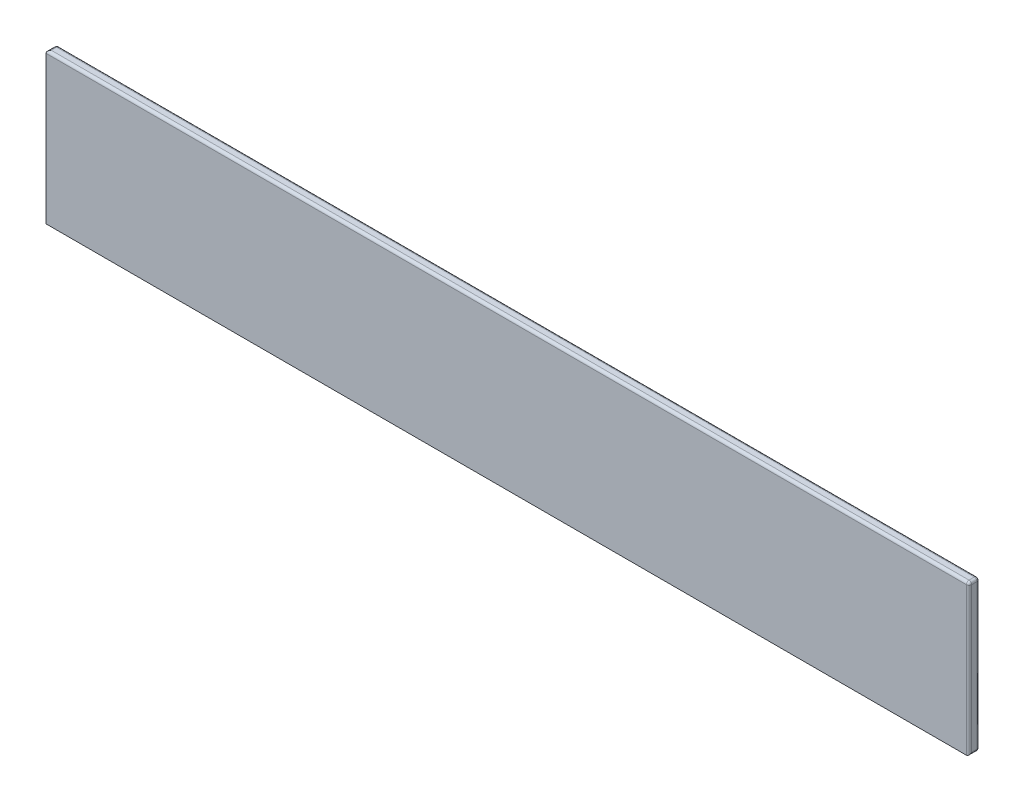
SolidWorks part; units mm, degrees
material "1060 Alloy"
ref_plane "Front Plane" through (0, 0, 0) normal (0, 0, 1) x (1, 0, 0)
ref_plane "Top Plane" through (0, 0, 0) normal (0, 1, 0) x (1, 0, 0)
ref_plane "Right Plane" through (0, 0, 0) normal (1, 0, 0) x (0, 0, -1)
sketch "Sketch1" plane through (0, 0, 0) normal (0, 0, 1) x (1, 0, 0)
  line L1 (-875, 142.5) -> (875, 142.5)
  line L2 (-875, 142.5) -> (-875, -142.5)
  line L3 (-875, -142.5) -> (875, -142.5)
  line L4 (875, 142.5) -> (875, -142.5)
  line L5 (-875, 142.5) -> (875, -142.5) construction
  line L6 (-875, -142.5) -> (875, 142.5) construction
  point P0 (0, 0)
  dimension "D1" = 285
  dimension "D2" = 1750
extrude "Boss-Extrude1" add sketch "Sketch1" along normal blind 20
fillet "Fillet1" radius 5 9 edges at (875, 0, 0) (0, 142.5, 0) (-875, 0, 0) (0, -142.5, 0) (875, 0, 20) (0, 142.5, 20) (875, -142.5, 10) (-875, 142.5, 10) (875, 142.5, 10)
